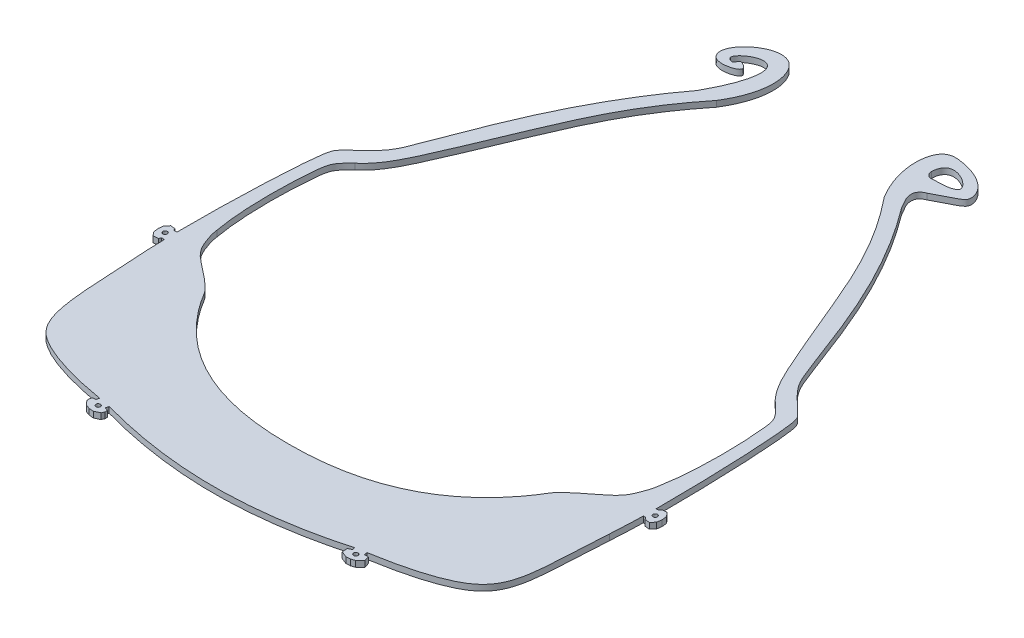
SolidWorks part; units mm, degrees
ref_plane "Front Plane" through (0, 0, 0) normal (0, 0, 1) x (1, 0, 0)
ref_plane "Top Plane" through (0, 0, 0) normal (0, 1, 0) x (1, 0, 0)
ref_plane "Right Plane" through (0, 0, 0) normal (1, 0, 0) x (0, 0, -1)
sketch "Sketch1" plane through (0, 0, 0) normal (0, 1, 0) x (1, 0, 0)
  line L0 (-56.7342, 4649.685) -> (-54.3432, 4649.8666)
  line L1 (-54.3432, 4649.8666) -> (-51.9673, 4650.1279)
  line L2 (-51.9673, 4650.1279) -> (-49.6128, 4650.4904)
  line L3 (-49.6128, 4650.4904) -> (-47.2873, 4650.9763)
  line L4 (-47.2873, 4650.9763) -> (-45.0028, 4651.606)
  line L5 (-45.0028, 4651.606) -> (-42.7754, 4652.393)
  line L6 (-42.7754, 4652.393) -> (-40.6236, 4653.3398)
  line L7 (-40.6236, 4653.3398) -> (-38.5569, 4654.4471)
  line L8 (-38.5569, 4654.4471) -> (-36.5628, 4655.7048)
  line L9 (-36.5628, 4655.7048) -> (-34.628, 4657.0886)
  line L10 (-34.628, 4657.0886) -> (-32.7572, 4658.5809)
  line L11 (-32.7572, 4658.5809) -> (-31.8781, 4659.3559)
  line L12 (-31.8781, 4659.3559) -> (-31.0378, 4660.1663)
  line L13 (-31.0378, 4660.1663) -> (-30.2434, 4661.0133)
  line L14 (-30.2434, 4661.0133) -> (-29.4929, 4661.8977)
  line L15 (-29.4929, 4661.8977) -> (-28.0377, 4663.8002)
  line L16 (-28.0377, 4663.8002) -> (-26.6418, 4665.7643)
  line L17 (-26.6418, 4665.7643) -> (-25.2842, 4667.7433)
  line L18 (-25.2842, 4667.7433) -> (-24.5616, 4668.7671)
  line L19 (-24.5616, 4668.7671) -> (-24.1207, 4669.3049)
  line L20 (-24.1207, 4669.3049) -> (-23.6287, 4669.8041)
  line L21 (-23.6287, 4669.8041) -> (-22.6527, 4670.6453)
  line L22 (-22.6527, 4670.6453) -> (-21.6624, 4671.4168)
  line L23 (-21.6624, 4671.4168) -> (-19.7154, 4672.8766)
  line L24 (-19.7154, 4672.8766) -> (-18.7888, 4673.6051)
  line L25 (-18.7888, 4673.6051) -> (-17.9151, 4674.3646)
  line L26 (-17.9151, 4674.3646) -> (-17.0961, 4675.1711)
  line L27 (-17.0961, 4675.1711) -> (-16.3332, 4676.0235)
  line L28 (-16.3332, 4676.0235) -> (-14.888, 4677.8872)
  line L29 (-14.888, 4677.8872) -> (-14.2651, 4678.8282)
  line L30 (-14.2651, 4678.8282) -> (-13.7395, 4679.8092)
  line L31 (-13.7395, 4679.8092) -> (-13.3157, 4680.8364)
  line L32 (-13.3157, 4680.8364) -> (-12.9921, 4681.9053)
  line L33 (-12.9921, 4681.9053) -> (-12.765, 4683.0137)
  line L34 (-12.765, 4683.0137) -> (-12.6116, 4684.156)
  line L35 (-12.6116, 4684.156) -> (-12.4221, 4686.5439)
  line L36 (-12.4221, 4686.5439) -> (-12.3049, 4688.9547)
  line L37 (-12.3049, 4688.9547) -> (-12.23, 4691.3606)
  line L38 (-12.23, 4691.3606) -> (-12.2173, 4693.7469)
  line L39 (-12.2173, 4693.7469) -> (-12.2979, 4696.128)
  line L40 (-12.2979, 4696.128) -> (-12.4621, 4698.525)
  line L41 (-12.4621, 4698.525) -> (-12.9016, 4703.3562)
  line L42 (-12.9016, 4703.3562) -> (-13.1725, 4705.7323)
  line L43 (-13.1725, 4705.7323) -> (-13.359, 4706.8497)
  line L44 (-13.359, 4706.8497) -> (-13.6464, 4707.8976)
  line L45 (-13.6464, 4707.8976) -> (-13.8331, 4708.3435)
  line L46 (-13.8331, 4708.3435) -> (-14.0727, 4708.7863)
  line L47 (-14.0727, 4708.7863) -> (-14.3603, 4709.2104)
  line L48 (-14.3603, 4709.2104) -> (-14.6922, 4709.6118)
  line L49 (-14.6922, 4709.6118) -> (-15.5352, 4710.4427)
  line L50 (-15.5352, 4710.4427) -> (-16.4733, 4711.2489)
  line L51 (-16.4733, 4711.2489) -> (-18.3969, 4712.8768)
  line L52 (-18.3969, 4712.8768) -> (-19.3317, 4713.7593)
  line L53 (-19.3317, 4713.7593) -> (-19.7964, 4714.2738)
  line L54 (-19.7964, 4714.2738) -> (-20.226, 4714.8564)
  line L55 (-20.226, 4714.8564) -> (-20.8491, 4716.0227)
  line L56 (-20.8491, 4716.0227) -> (-21.3607, 4717.2182)
  line L57 (-21.3607, 4717.2182) -> (-22.2565, 4719.6128)
  line L58 (-22.2565, 4719.6128) -> (-23.9365, 4724.4003)
  line L59 (-23.9365, 4724.4003) -> (-24.8142, 4726.6925)
  line L60 (-24.8142, 4726.6925) -> (-25.7235, 4728.951)
  line L61 (-25.7235, 4728.951) -> (-29.4192, 4737.978)
  line L62 (-29.4192, 4737.978) -> (-31.3112, 4742.476)
  line L63 (-31.3112, 4742.476) -> (-32.3108, 4744.6883)
  line L64 (-32.3108, 4744.6883) -> (-33.3653, 4746.8748)
  line L65 (-33.3653, 4746.8748) -> (-34.484, 4749.0197)
  line L66 (-34.484, 4749.0197) -> (-35.6822, 4751.1089)
  line L67 (-35.6822, 4751.1089) -> (-36.9697, 4753.1376)
  line L68 (-36.9697, 4753.1376) -> (-38.335, 4755.1176)
  line L69 (-38.335, 4755.1176) -> (-39.7566, 4757.0561)
  line L70 (-39.7566, 4757.0561) -> (-41.2239, 4758.9538)
  line L71 (-41.2239, 4758.9538) -> (-44.2837, 4762.6862)
  line L72 (-44.2837, 4762.6862) -> (-45.0093, 4763.5782)
  line L73 (-45.7102, 4766.0333) -> (-45.6003, 4766.895)
  line L74 (-44.3387, 4767.2717) -> (-41.5099, 4763.9631)
  line L75 (-41.5099, 4763.9631) -> (-39.7615, 4761.7893)
  line L76 (-39.7615, 4761.7893) -> (-36.1552, 4757.1077)
  line L77 (-36.1552, 4757.1077) -> (-34.4224, 4754.6956)
  line L78 (-34.4224, 4754.6956) -> (-32.818, 4752.1875)
  line L79 (-32.818, 4752.1875) -> (-31.4001, 4749.5854)
  line L80 (-31.4001, 4749.5854) -> (-30.1172, 4746.945)
  line L81 (-30.1172, 4746.945) -> (-27.7453, 4741.6402)
  line L82 (-27.7453, 4741.6402) -> (-25.4835, 4736.2816)
  line L83 (-25.4835, 4736.2816) -> (-23.2904, 4730.8724)
  line L84 (-23.2904, 4730.8724) -> (-21.1708, 4725.4153)
  line L85 (-21.1708, 4725.4153) -> (-19.1018, 4719.943)
  line L86 (-19.1018, 4719.943) -> (-18.1004, 4717.2034)
  line L87 (-18.1004, 4717.2034) -> (-17.875, 4716.5966)
  line L88 (-17.875, 4716.5966) -> (-17.6236, 4716.1359)
  line L89 (-17.6236, 4716.1359) -> (-17.2675, 4715.7336)
  line L90 (-17.2675, 4715.7336) -> (-16.7845, 4715.2999)
  line L91 (-16.7845, 4715.2999) -> (-14.566, 4713.4273)
  line L92 (-14.566, 4713.4273) -> (-13.4359, 4712.453)
  line L93 (-13.4359, 4712.453) -> (-12.2875, 4711.3506)
  line L94 (-12.2875, 4711.3506) -> (-11.7288, 4710.5494)
  line L95 (-11.7288, 4710.5494) -> (-11.4049, 4709.6505)
  line L96 (-11.4049, 4709.6505) -> (-11.1035, 4708.0976)
  line L97 (-11.1035, 4708.0976) -> (-10.7039, 4705.1867)
  line L98 (-10.7039, 4705.1867) -> (-10.3782, 4702.2301)
  line L99 (-10.3782, 4702.2301) -> (-10.1381, 4699.312)
  line L100 (-10.1381, 4699.312) -> (-9.9526, 4696.4059)
  line L101 (-9.9526, 4696.4059) -> (-9.8234, 4693.4642)
  line L102 (-9.8234, 4693.4642) -> (-9.7818, 4690.5097)
  line L103 (-9.7818, 4690.5097) -> (-9.8395, 4687.5651)
  line L104 (-9.8395, 4687.5651) -> (-10.1467, 4681.8499)
  line L105 (-10.2187, 4680.4106) -> (-10.5778, 4674.8324)
  line L106 (-10.5778, 4674.8324) -> (-10.9255, 4669.1921)
  line L107 (-10.9255, 4669.1921) -> (-11.1085, 4666.3239)
  line L108 (-11.1085, 4666.3239) -> (-11.3672, 4663.3976)
  line L109 (-11.3672, 4663.3976) -> (-11.5954, 4661.8877)
  line L110 (-11.5954, 4661.8877) -> (-11.9481, 4660.3817)
  line L111 (-11.9481, 4660.3817) -> (-12.469, 4658.9063)
  line L112 (-12.469, 4658.9063) -> (-13.1768, 4657.5086)
  line L113 (-13.1768, 4657.5086) -> (-14.0475, 4656.2056)
  line L114 (-14.0475, 4656.2056) -> (-15.0678, 4655.0233)
  line L115 (-15.0678, 4655.0233) -> (-15.6664, 4654.4674)
  line L116 (-15.6664, 4654.4674) -> (-16.3022, 4653.9611)
  line L117 (-16.3022, 4653.9611) -> (-17.6055, 4653.1269)
  line L118 (-17.6055, 4653.1269) -> (-18.9712, 4652.4383)
  line L119 (-18.9712, 4652.4383) -> (-20.3502, 4651.8561)
  line L120 (-20.3502, 4651.8561) -> (-21.7405, 4651.3486)
  line L121 (-21.7405, 4651.3486) -> (-23.1491, 4650.8937)
  line L122 (-23.1491, 4650.8937) -> (-25.9685, 4650.1281)
  line L123 (-25.9685, 4650.1281) -> (-28.8127, 4649.495)
  line L124 (-28.8127, 4649.495) -> (-34.3611, 4648.4388)
  line L125 (-35.7786, 4648.1905) -> (-42.1243, 4647.1501)
  line L126 (-42.1243, 4647.1501) -> (-45.3893, 4646.7207)
  line L127 (-45.3893, 4646.7207) -> (-48.6635, 4646.3827)
  line L128 (-48.6635, 4646.3827) -> (-55.1892, 4645.922)
  line L129 (-55.1892, 4645.922) -> (-61.7354, 4645.5886)
  line L130 (-61.7354, 4645.5886) -> (-63.9666, 4645.5453)
  line L131 (-63.9667, 4649.4865) -> (-59.1315, 4649.5688)
  line L132 (-59.1315, 4649.5688) -> (-56.7342, 4649.685)
  line L133 (-9.7721, 4681.8294) -> (-9.752, 4682.186)
  line L134 (-9.752, 4682.186) -> (-9.3693, 4682.5229)
  line L135 (-9.3693, 4682.5229) -> (-8.649, 4682.4768)
  line L136 (-8.649, 4682.4768) -> (-7.9775, 4681.713)
  line L137 (-7.9775, 4681.713) -> (-8.2411, 4680.2884)
  line L138 (-8.2411, 4680.2884) -> (-9.0059, 4679.6162)
  line L139 (-9.0059, 4679.6162) -> (-9.5491, 4679.6473)
  line L140 (-9.5491, 4679.6473) -> (-9.8867, 4680.0303)
  line L141 (-9.8867, 4680.0303) -> (-9.8664, 4680.3889)
  line L142 (-9.7721, 4681.8294) -> (-9.752, 4682.186)
  line L151 (-34.2991, 4648.0806) -> (-33.9447, 4648.1421)
  line L152 (-33.9447, 4648.1421) -> (-33.5285, 4647.8485)
  line L153 (-33.5285, 4647.8485) -> (-33.4056, 4647.1395)
  line L154 (-33.4056, 4647.1395) -> (-33.9931, 4646.3074)
  line L155 (-33.9931, 4646.3074) -> (-35.4108, 4646.0612)
  line L156 (-35.4108, 4646.0612) -> (-36.2441, 4646.6493)
  line L157 (-36.2441, 4646.6493) -> (-36.3669, 4647.358)
  line L158 (-36.3669, 4647.358) -> (-36.0733, 4647.7743)
  line L159 (-36.0733, 4647.7743) -> (-35.7187, 4647.8357)
  line L160 (-10.1467, 4681.8499) -> (-9.7721, 4681.8294)
  line L161 (-34.3611, 4648.4388) -> (-34.2991, 4648.0806)
  line L162 (-35.7786, 4648.1905) -> (-35.7187, 4647.8357)
  line L163 (-9.8664, 4680.3889) -> (-10.2187, 4680.4106)
  line L165 (-118.1813, 4682.186) -> (-118.5641, 4682.5226)
  line L166 (-118.5641, 4682.5226) -> (-119.2843, 4682.4768)
  line L167 (-119.2843, 4682.4768) -> (-119.9558, 4681.7128)
  line L168 (-119.9558, 4681.7128) -> (-119.8643, 4680.2786)
  line L169 (-119.8643, 4680.2786) -> (-119.0995, 4679.6064)
  line L170 (-119.0995, 4679.6064) -> (-118.3843, 4679.6471)
  line L171 (-118.3843, 4679.6471) -> (-118.0466, 4680.0303)
  line L172 (-118.0466, 4680.0303) -> (-118.0672, 4680.3889)
  line L173 (-118.0672, 4680.3889) -> (-117.7148, 4680.4103)
  line L174 (-117.7148, 4680.4103) -> (-117.3555, 4674.8322)
  line L175 (-117.3555, 4674.8322) -> (-117.0078, 4669.1921)
  line L176 (-117.0078, 4669.1921) -> (-116.8249, 4666.3237)
  line L177 (-116.8249, 4666.3237) -> (-116.566, 4663.3974)
  line L178 (-116.566, 4663.3974) -> (-116.3378, 4661.8875)
  line L179 (-116.3378, 4661.8875) -> (-115.9851, 4660.3817)
  line L180 (-115.9851, 4660.3817) -> (-115.4645, 4658.906)
  line L181 (-115.4645, 4658.906) -> (-114.7563, 4657.5086)
  line L182 (-114.7563, 4657.5086) -> (-113.8857, 4656.2053)
  line L183 (-113.8857, 4656.2053) -> (-112.8656, 4655.0233)
  line L184 (-112.8656, 4655.0233) -> (-112.2669, 4654.4674)
  line L185 (-112.2669, 4654.4674) -> (-111.6311, 4653.9608)
  line L186 (-111.6311, 4653.9608) -> (-110.328, 4653.1269)
  line L187 (-110.328, 4653.1269) -> (-108.9621, 4652.4383)
  line L188 (-108.9621, 4652.4383) -> (-107.5832, 4651.8561)
  line L189 (-107.5832, 4651.8561) -> (-106.1928, 4651.3484)
  line L190 (-106.1928, 4651.3484) -> (-104.7844, 4650.8937)
  line L191 (-104.7844, 4650.8937) -> (-101.9649, 4650.1279)
  line L192 (-101.9649, 4650.1279) -> (-99.1205, 4649.4948)
  line L193 (-99.1205, 4649.4948) -> (-93.5721, 4648.4388)
  line L194 (-93.5721, 4648.4388) -> (-93.6341, 4648.0806)
  line L195 (-93.6341, 4648.0806) -> (-93.9885, 4648.1421)
  line L196 (-93.9885, 4648.1421) -> (-94.4046, 4647.8485)
  line L197 (-94.4046, 4647.8485) -> (-94.5276, 4647.1392)
  line L198 (-94.5276, 4647.1392) -> (-93.9404, 4646.3074)
  line L199 (-93.9404, 4646.3074) -> (-92.5223, 4646.0612)
  line L200 (-92.5223, 4646.0612) -> (-91.6891, 4646.6493)
  line L201 (-91.6891, 4646.6493) -> (-91.5662, 4647.358)
  line L202 (-91.5662, 4647.358) -> (-91.8598, 4647.7743)
  line L203 (-91.8598, 4647.7743) -> (-92.2145, 4647.8357)
  line L204 (-92.1546, 4648.1905) -> (-92.2145, 4647.8357)
  line L205 (-92.1546, 4648.1905) -> (-85.8089, 4647.1501)
  line L206 (-85.8089, 4647.1501) -> (-82.5441, 4646.7204)
  line L207 (-82.5441, 4646.7204) -> (-79.2698, 4646.3827)
  line L208 (-79.2698, 4646.3827) -> (-72.7439, 4645.922)
  line L209 (-72.7439, 4645.922) -> (-66.1978, 4645.5886)
  line L210 (-66.1978, 4645.5886) -> (-63.9666, 4645.5453)
  line L211 (-63.9667, 4649.4865) -> (-68.8018, 4649.5688)
  line L212 (-68.8018, 4649.5688) -> (-71.1991, 4649.685)
  line L213 (-71.1991, 4649.685) -> (-73.5901, 4649.8666)
  line L214 (-73.5901, 4649.8666) -> (-75.9659, 4650.1279)
  line L215 (-75.9659, 4650.1279) -> (-78.3204, 4650.4904)
  line L216 (-78.3204, 4650.4904) -> (-80.646, 4650.976)
  line L217 (-80.646, 4650.976) -> (-82.9304, 4651.606)
  line L218 (-82.9304, 4651.606) -> (-85.1578, 4652.393)
  line L219 (-85.1578, 4652.393) -> (-87.3097, 4653.3398)
  line L220 (-87.3097, 4653.3398) -> (-89.3762, 4654.4469)
  line L221 (-89.3762, 4654.4469) -> (-91.3704, 4655.7045)
  line L222 (-91.3704, 4655.7045) -> (-93.3054, 4657.0883)
  line L223 (-93.3054, 4657.0883) -> (-95.1761, 4658.5809)
  line L224 (-95.1761, 4658.5809) -> (-96.0551, 4659.3559)
  line L225 (-96.0551, 4659.3559) -> (-96.8955, 4660.1661)
  line L226 (-96.8955, 4660.1661) -> (-97.6899, 4661.013)
  line L227 (-97.6899, 4661.013) -> (-98.4405, 4661.8974)
  line L228 (-98.4405, 4661.8974) -> (-99.8956, 4663.8003)
  line L229 (-99.8956, 4663.8003) -> (-101.2917, 4665.7643)
  line L230 (-101.2917, 4665.7643) -> (-102.649, 4667.7433)
  line L231 (-102.649, 4667.7433) -> (-103.3717, 4668.7671)
  line L232 (-103.3717, 4668.7671) -> (-103.8126, 4669.3049)
  line L233 (-103.8126, 4669.3049) -> (-104.3045, 4669.8038)
  line L234 (-104.3045, 4669.8038) -> (-105.2805, 4670.645)
  line L235 (-105.2805, 4670.645) -> (-106.2711, 4671.4168)
  line L236 (-106.2711, 4671.4168) -> (-108.218, 4672.8766)
  line L237 (-108.218, 4672.8766) -> (-109.1446, 4673.6051)
  line L238 (-109.1446, 4673.6051) -> (-110.0184, 4674.3646)
  line L239 (-110.0184, 4674.3646) -> (-110.8371, 4675.1711)
  line L240 (-110.8371, 4675.1711) -> (-111.6001, 4676.0232)
  line L241 (-111.6001, 4676.0232) -> (-113.0454, 4677.8872)
  line L242 (-113.0454, 4677.8872) -> (-113.6683, 4678.8282)
  line L243 (-113.6683, 4678.8282) -> (-114.1938, 4679.8092)
  line L244 (-114.1938, 4679.8092) -> (-114.6176, 4680.8364)
  line L245 (-114.6176, 4680.8364) -> (-114.9413, 4681.905)
  line L246 (-114.9413, 4681.905) -> (-115.1684, 4683.0135)
  line L247 (-115.1684, 4683.0135) -> (-115.3218, 4684.156)
  line L248 (-115.3218, 4684.156) -> (-115.5115, 4686.5436)
  line L249 (-115.5115, 4686.5436) -> (-115.6283, 4688.9545)
  line L250 (-115.6283, 4688.9545) -> (-115.7033, 4691.3606)
  line L251 (-115.7033, 4691.3606) -> (-115.7161, 4693.7466)
  line L252 (-115.7161, 4693.7466) -> (-115.6355, 4696.1278)
  line L253 (-115.6355, 4696.1278) -> (-115.4714, 4698.525)
  line L254 (-115.4714, 4698.525) -> (-115.0316, 4703.3562)
  line L255 (-115.0316, 4703.3562) -> (-114.7608, 4705.732)
  line L256 (-114.7608, 4705.732) -> (-114.5743, 4706.8497)
  line L257 (-114.5743, 4706.8497) -> (-114.287, 4707.8977)
  line L258 (-114.287, 4707.8977) -> (-114.1002, 4708.3435)
  line L259 (-114.1002, 4708.3435) -> (-113.8608, 4708.7862)
  line L260 (-113.8608, 4708.7862) -> (-113.5731, 4709.2103)
  line L261 (-113.5731, 4709.2103) -> (-113.2411, 4709.6117)
  line L262 (-113.2411, 4709.6117) -> (-112.3981, 4710.4425)
  line L263 (-112.3981, 4710.4425) -> (-111.4599, 4711.2487)
  line L264 (-111.4599, 4711.2487) -> (-109.5364, 4712.8767)
  line L265 (-109.5364, 4712.8767) -> (-108.602, 4713.7592)
  line L266 (-108.602, 4713.7592) -> (-108.1369, 4714.2737)
  line L267 (-108.1369, 4714.2737) -> (-107.7072, 4714.8564)
  line L268 (-107.7072, 4714.8564) -> (-107.0842, 4716.0225)
  line L269 (-107.0842, 4716.0225) -> (-106.5727, 4717.2181)
  line L270 (-106.5727, 4717.2181) -> (-105.6769, 4719.6127)
  line L271 (-105.6769, 4719.6127) -> (-103.9969, 4724.4001)
  line L272 (-103.9969, 4724.4001) -> (-103.1193, 4726.6924)
  line L273 (-103.1193, 4726.6924) -> (-102.2099, 4728.9509)
  line L274 (-102.2099, 4728.9509) -> (-98.5143, 4737.9778)
  line L275 (-98.5143, 4737.9778) -> (-96.6221, 4742.4757)
  line L276 (-96.6221, 4742.4757) -> (-95.6227, 4744.6884)
  line L277 (-95.6227, 4744.6884) -> (-94.5682, 4746.8748)
  line L278 (-94.5682, 4746.8748) -> (-93.4493, 4749.0197)
  line L279 (-93.4493, 4749.0197) -> (-92.2515, 4751.1088)
  line L280 (-92.2515, 4751.1088) -> (-90.9637, 4753.1374)
  line L281 (-90.9637, 4753.1374) -> (-89.5985, 4755.1174)
  line L282 (-89.5985, 4755.1174) -> (-88.177, 4757.0561)
  line L283 (-88.177, 4757.0561) -> (-86.7094, 4758.9538)
  line L284 (-86.7094, 4758.9538) -> (-83.65, 4762.6862)
  line L285 (-83.65, 4762.6862) -> (-82.924, 4763.5782)
  line L286 (-82.2232, 4766.0334) -> (-82.3333, 4766.8949)
  line L287 (-83.5948, 4767.2716) -> (-86.4235, 4763.963)
  line L288 (-86.4235, 4763.963) -> (-88.172, 4761.7894)
  line L289 (-88.172, 4761.7894) -> (-91.7784, 4757.1074)
  line L290 (-91.7784, 4757.1074) -> (-93.5112, 4754.6958)
  line L291 (-93.5112, 4754.6958) -> (-95.1154, 4752.1875)
  line L292 (-95.1154, 4752.1875) -> (-96.5333, 4749.5852)
  line L293 (-96.5333, 4749.5852) -> (-97.8162, 4746.9449)
  line L294 (-97.8162, 4746.9449) -> (-100.1881, 4741.6403)
  line L295 (-100.1881, 4741.6403) -> (-102.4501, 4736.2814)
  line L296 (-102.4501, 4736.2814) -> (-104.6429, 4730.8726)
  line L297 (-104.6429, 4730.8726) -> (-106.7626, 4725.415)
  line L298 (-106.7626, 4725.415) -> (-108.8314, 4719.9429)
  line L299 (-108.8314, 4719.9429) -> (-109.8329, 4717.2035)
  line L300 (-109.8329, 4717.2035) -> (-110.0583, 4716.5964)
  line L301 (-110.0583, 4716.5964) -> (-110.3097, 4716.1357)
  line L302 (-110.3097, 4716.1357) -> (-110.6661, 4715.7335)
  line L303 (-110.6661, 4715.7335) -> (-111.1489, 4715.2998)
  line L304 (-111.1489, 4715.2998) -> (-113.3676, 4713.4272)
  line L305 (-113.3676, 4713.4272) -> (-114.4976, 4712.4528)
  line L306 (-114.4976, 4712.4528) -> (-115.646, 4711.3505)
  line L307 (-115.646, 4711.3505) -> (-116.2044, 4710.5493)
  line L308 (-116.2044, 4710.5493) -> (-116.5286, 4709.6504)
  line L309 (-116.5286, 4709.6504) -> (-116.8298, 4708.0975)
  line L310 (-116.8298, 4708.0975) -> (-117.2296, 4705.1868)
  line L311 (-117.2296, 4705.1868) -> (-117.5553, 4702.2301)
  line L312 (-117.5553, 4702.2301) -> (-117.7952, 4699.312)
  line L313 (-117.7952, 4699.312) -> (-117.981, 4696.4059)
  line L314 (-117.981, 4696.4059) -> (-118.11, 4693.4642)
  line L315 (-118.11, 4693.4642) -> (-118.1516, 4690.5097)
  line L316 (-118.1516, 4690.5097) -> (-118.0939, 4687.5649)
  line L317 (-118.0939, 4687.5649) -> (-117.7865, 4681.8497)
  line L318 (-117.7865, 4681.8497) -> (-118.1612, 4681.8294)
  line L319 (-118.1612, 4681.8294) -> (-118.1813, 4682.186)
  spline S0 degree 3 poles (-45.7102, 4766.0333) (-45.8224, 4765.1537) (-45.5692, 4764.2663) (-45.0093, 4763.5782) knots 0 0 0 0 1 1 1 1
  spline S1 degree 3 poles (-44.3387, 4767.2717) (-44.5973, 4767.574) (-45.0517, 4767.6095) (-45.3539, 4767.351) knots 0 0 0 0 1 1 1 1
  spline S2 degree 3 poles (-45.3539, 4767.351) (-45.4898, 4767.2349) (-45.5777, 4767.0723) (-45.6003, 4766.895) knots 0 0 0 0 1 1 1 1
  spline S3 degree 3 poles (-82.924, 4763.5782) (-82.3642, 4764.2661) (-82.111, 4765.1536) (-82.2232, 4766.0334) knots 0 0 0 0 1 1 1 1
  spline S4 degree 3 poles (-82.3333, 4766.8949) (-82.3835, 4767.2894) (-82.7441, 4767.5683) (-83.1386, 4767.518) knots 0 0 0 0 1 1 1 1
  spline S5 degree 3 poles (-83.1386, 4767.518) (-83.3159, 4767.4954) (-83.4785, 4767.4075) (-83.5948, 4767.2716) knots 0 0 0 0 1 1 1 1
sketch "Sketch2" plane through (0, 0, 0) normal (0, 1, 0) x (1, 0, 0)
  line L0 (-63.9234, 4631.4262) -> (-63.9234, 4609.4594) construction
  line L25 (-22.4985, 4637.3551) -> (-18.9434, 4638.0357) construction
  line L26 (-20.7209, 4637.6954) -> (-20.3316, 4635.6618) construction
  line L31 (-16.9423, 4635.297) -> (-18.5347, 4633.796)
  line L32 (-20.3316, 4635.6618) -> (-19.8467, 4633.1287) construction
  line L33 (-18.5347, 4633.796) -> (-19.8873, 4633.3404)
  line L34 (-21.3125, 4633.2642) -> (-19.8873, 4633.3404)
  line L35 (-23.3466, 4634.071) -> (-21.3125, 4633.2642)
  line L40 (-104.4735, 4635.7404) -> (-104.4735, 4634.9567)
  line L41 (-104.4735, 4634.9567) -> (-104.8805, 4633.998)
  line L42 (-104.8805, 4633.998) -> (-106.6203, 4633.1744)
  line L43 (-106.6203, 4633.1744) -> (-108.2043, 4633.2927)
  line L44 (-109.6975, 4633.8343) -> (-108.2043, 4633.2927)
  line L45 (-110.9466, 4635.2989) -> (-109.6975, 4633.8343)
  line L46 (-110.9246, 4636.3402) -> (-110.9466, 4635.2989)
  line L47 (-110.6737, 4637.0191) -> (-110.9246, 4636.3402)
  line L49 (-146.8202, 4697.6298) -> (-149.3915, 4697.5949) construction
  line L50 (16.9036, 4697.658) -> (18.9735, 4697.6298) construction
  line L54 (20.0716, 4700.6062) -> (21.1812, 4699.2558)
  line L55 (18.9735, 4697.6298) -> (21.5448, 4697.5949) construction
  line L56 (21.1812, 4699.2558) -> (21.376, 4697.5972)
  line L57 (21.1362, 4695.9445) -> (21.376, 4697.5972)
  line L58 (19.9903, 4694.6247) -> (21.1362, 4695.9445)
  line L62 (-144.7504, 4697.658) -> (-146.8202, 4697.6298) construction
  line L67 (-148.983, 4695.9445) -> (-149.2228, 4697.5972)
  line L68 (-149.028, 4699.2558) -> (-149.2228, 4697.5972)
  line L69 (-147.9184, 4700.6062) -> (-149.028, 4699.2558)
  line L73 (18.4279, 4700.4703) -> (20.0716, 4700.6062)
  line L74 (18.3509, 4694.8052) -> (19.9903, 4694.6247)
  line L75 (-23.4805, 4635.8657) -> (-23.3466, 4634.071)
  line L76 (-17.4807, 4637.0143) -> (-16.9423, 4635.297)
  line L77 (-32.2984, 4843.1108) -> (-32.9734, 4843.0745)
  line L79 (-146.2747, 4700.4703) -> (-146.0774, 4699.7908)
  line L80 (-146.0774, 4699.7908) -> (-144.9978, 4699.7908)
  line L81 (-146.1977, 4694.8052) -> (-145.9394, 4695.5191)
  line L82 (-145.9394, 4695.5191) -> (-144.9397, 4695.5191)
  line L83 (-110.6737, 4637.0191) -> (-109.7005, 4637.0191)
  line L84 (-109.7005, 4637.0191) -> (-109.3372, 4638.0212)
  line L85 (-104.4735, 4635.7404) -> (-105.6297, 4636.1595)
  line L86 (-105.6297, 4636.1595) -> (-105.3482, 4637.2394)
  line L87 (-23.4805, 4635.8657) -> (-22.2692, 4636.4725)
  line L88 (-22.2692, 4636.4725) -> (-22.4985, 4637.3551)
  line L89 (-17.4807, 4637.0143) -> (-18.7231, 4637.0143)
  line L90 (-18.7231, 4637.0143) -> (-18.9434, 4638.0357)
  line L91 (17.093, 4695.5191) -> (17.927, 4695.5191)
  line L92 (17.927, 4695.5191) -> (18.3509, 4694.8052)
  line L93 (17.151, 4699.7908) -> (17.9273, 4699.7908)
  line L94 (17.9273, 4699.7908) -> (18.4279, 4700.4703)
  line L95 (-147.9184, 4700.6062) -> (-146.2747, 4700.4703)
  line L96 (-148.983, 4695.9445) -> (-147.9184, 4694.6247)
  line L97 (-147.9184, 4694.6247) -> (-146.1977, 4694.8052)
  circle A0 centre (28.2666, 4698.0399) radius 0.5
  circle A1 centre (-20.3316, 4635.6618) radius 0.75
  circle A2 centre (-107.5151, 4635.6618) radius 0.75
  circle A4 centre (18.9735, 4697.6298) radius 0.75
  circle A5 centre (-146.8202, 4697.6298) radius 0.75
  arc A7 (-35.0807, 4845.0881) -> (-32.9734, 4843.0745) centre (-33.0807, 4845.0716) ccw
  spline S0 degree 3 poles (-105.3482, 4637.2394) (-91.774, 4633.4496) (-63.9165, 4629.3481) (-36.075, 4633.5591) (-22.4985, 4637.3551) knots 0.018742 0.018742 0.018742 0.018742 0.500293 0.981945 0.981945 0.981945 0.981945
  spline S1 degree 3 poles (-18.9434, 4638.0357) (-9.0248, 4639.6859) (4.6467, 4643.0604) (16.372, 4654.3944) (15.2524, 4666.3346) (16.6172, 4684.5147) knots 0.018902 0.018902 0.018902 0.018902 0.394122 0.490995 0.987629 0.987629 0.987629 0.987629
  spline S2 degree 3 poles (16.6172, 4684.5147) (16.7593, 4687.5885) (17.0552, 4691.3248) (17.093, 4695.5191) knots 0.004735 0.004735 0.004735 0.004735 0.035162 0.035162 0.035162 0.035162
  spline S3 degree 3 poles (17.151, 4699.7908) (17.187, 4718.7532) (15.9463, 4748.1489) (12.9962, 4752.2096) (5.5902, 4758.1445) (-2.0809, 4776.0395) (-10.7699, 4804.5442) (-29.3841, 4829.3082) knots 0.04445 0.04445 0.04445 0.04445 0.175223 0.204985 0.326837 0.407861 1 1 1 1
  spline S4 degree 2 poles (-63.9234, 4656.5726) (-23.3221, 4656.4521) (-5.293, 4686.6697) knots 0 0 0 1 1 1
  spline S5 degree 3 poles (-5.293, 4686.6697) (-3.3882, 4689.5147) (5.5322, 4695.6316) (7.0158, 4697.627) (8.9185, 4699.9572) (10.6489, 4704.6448) (10.9298, 4707.0618) knots 0 0 0 0 0.517385 0.711984 0.762678 1 1 1 1
  spline S6 degree 3 poles (10.9298, 4707.0618) (12.5257, 4715.666) (12.951, 4730.9053) (11.2091, 4746.2487) (8.6834, 4748.7091) (7.186, 4750.111) knots 0 0 0 0 0.7977 0.8977 1 1 1 1
  spline S7 degree 3 poles (7.186, 4750.111) (2.646, 4753.9155) (-14.478, 4791.0238) (-18.8641, 4808.8265) (-35.5523, 4829.6542) knots 0 0 0 0 0.147118 0.925748 0.925748 0.925748 0.925748
  spline S8 degree 3 poles (-29.3841, 4829.3082) (-30.2798, 4830.9279) (-32.3375, 4833.6012) (-31.9186, 4837.1985) (-29.5772, 4838.0674) knots 0 0 0 0 0.008449 0.016898 0.016898 0.016898 0.016898
  spline S9 degree 3 poles (-98.4627, 4829.3082) (-93.3382, 4838.5746) (-90.1955, 4855.0632) (-104.8701, 4845.5685) (-99.3126, 4842.3191) (-101.0297, 4847.0369) (-95.5318, 4842.3824) (-104.1746, 4840.111) (-108.4842, 4847.9039) (-89.3943, 4862.5447) (-85.2547, 4840.9598) (-92.2945, 4829.6542) knots 0 0 0 0 0.089848 0.265685 0.309991 0.508137 0.54443 0.63662 0.668771 0.85442 1 1 1 1
  spline S10 degree 3 poles (-135.0327, 4750.111) (-130.4928, 4753.9155) (-113.3687, 4791.0238) (-108.9827, 4808.8265) (-92.2945, 4829.6542) knots 0 0 0 0 0.147118 0.925748 0.925748 0.925748 0.925748
  spline S11 degree 3 poles (-138.7766, 4707.0618) (-140.3724, 4715.666) (-140.7978, 4730.9053) (-139.0558, 4746.2487) (-136.5302, 4748.7091) (-135.0327, 4750.111) knots 0 0 0 0 0.7977 0.8977 1 1 1 1
  spline S12 degree 3 poles (-122.5537, 4686.6697) (-124.4586, 4689.5147) (-133.3789, 4695.6316) (-134.8625, 4697.627) (-136.7653, 4699.9572) (-138.4957, 4704.6448) (-138.7766, 4707.0618) knots 0 0 0 0 0.517385 0.711984 0.762678 1 1 1 1
  spline S13 degree 2 poles (-63.9234, 4656.5726) (-104.5246, 4656.4521) (-122.5537, 4686.6697) knots 0 0 0 1 1 1
  spline S14 degree 3 poles (-144.7494, 4689.4807) (-144.8339, 4691.3079) (-144.8968, 4693.3424) (-144.9397, 4695.5191) knots 0.004735 0.004735 0.004735 0.004735 0.022822 0.022822 0.022822 0.022822
  spline S15 degree 3 poles (-109.3372, 4638.0212) (-119.1435, 4639.6853) (-132.6028, 4643.2518) (-144.26, 4654.2895) (-143.3596, 4671.4378) (-144.7494, 4689.4807) knots 0.024856 0.024856 0.024856 0.024856 0.394717 0.491493 0.992616 0.992616 0.992616 0.992616
  spline S16 degree 3 poles (-35.0807, 4845.0881) (-35.0752, 4845.7469) (-34.0546, 4853.0999) (-22.8029, 4845.8756) (-27.2135, 4843.0601) (-30.5037, 4843.2073) (-32.2984, 4843.1108) knots 0.039445 0.039445 0.039445 0.039445 0.047752 0.136146 0.152448 0.210778 0.210778 0.210778 0.210778
  spline S17 degree 3 poles (-29.5772, 4838.0674) (-27.5451, 4839.1271) (-21.3795, 4842.0221) (-19.6275, 4845.3656) (-23.6456, 4852.3861) (-41.3765, 4854.0288) (-41.8881, 4839.8292) (-35.5523, 4829.6542) knots 0.329046 0.329046 0.329046 0.329046 0.434682 0.485511 0.79824 0.853598 1 1 1 1
  spline S18 degree 3 poles (-144.9978, 4699.7908) (-145.1407, 4717.9008) (-143.9805, 4747.7816) (-140.9459, 4752.3433) (-133.5185, 4758.0955) (-125.8345, 4776.2473) (-117.0769, 4804.5442) (-98.4627, 4829.3082) knots 0.034256 0.034256 0.034256 0.034256 0.174203 0.204985 0.326837 0.407861 1 1 1 1
  point P3 (-21.3125, 4842.579)
  point P71 (-29.5772, 4838.0674)
  point P95 (0, 0)
  point P97 (-99.4837, 4842.6063)
  point P98 (0, 0)
  point P103 (-98.6902, 4843.8679)
  point P110 (-97.2807, 4843.6664)
  point P114 (0, 0)
  point P117 (0, 0)
  point P118 (-29.3841, 4839.6297)
  point P119 (0, 0)
  point P120 (-30.2827, 4838.8077)
  point P121 (0, 0)
  point P122 (0, 0)
  point P123 (-32.5291, 4836.1312)
  point P124 (0, 0)
  point P125 (0, 0)
  point P126 (0, 0)
  dimension "D1" = 1
extrude "Boss-Extrude2" add sketch "Sketch2" along normal blind 2 separate body
